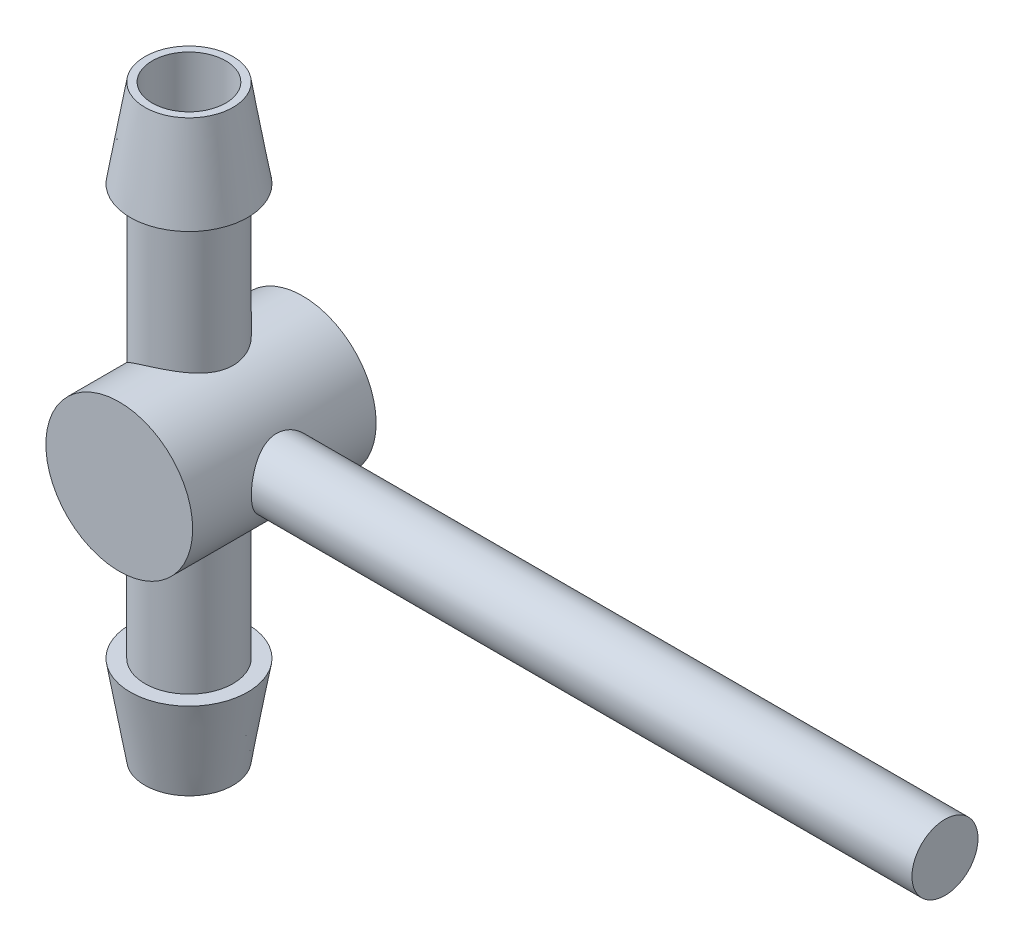
SolidWorks part; units mm, degrees
ref_plane "Front Plane" through (0, 0, 0) normal (0, 0, 1) x (1, 0, 0)
ref_plane "Top Plane" through (0, 0, 0) normal (0, 1, 0) x (1, 0, 0)
ref_plane "Right Plane" through (0, 0, 0) normal (1, 0, 0) x (0, 0, -1)
sketch "Sketch1" plane through (0, 0, 0) normal (0, 0, 1) x (1, 0, 0)
  circle A0 centre (0, 0) radius 5
  dimension "D1" = 10
extrude "Boss-Extrude1" add sketch "Sketch1" along normal mid plane 12.5
sketch "Sketch2" plane through (0, 0, 0) normal (0, 1, 0) x (1, 0, 0)
  line L0 (-5, 6.25) -> (-5, -6.25) construction
  circle A0 centre (-1.5, 0) radius 3
  point P2 (0, 0)
  point P3 (0, 0)
  point P4 (0, 0)
  point P5 (0, 0)
  dimension "D1" = 6
  dimension "D2" = 3.5
extrude "Boss-Extrude2" add sketch "Sketch2" along normal mid plane 40
sketch "Sketch3" plane through (0, 0, 0) normal (1, 0, 0) x (0, 0, -1)
  circle A0 centre (0, 0) radius 2.25
  dimension "D1" = 4.5
extrude "Boss-Extrude3" add sketch "Sketch3" along normal blind 50
sketch "Sketch4" plane through (0, -20, 0) normal (0, -1, 0) x (1, 0, 0)
  line L0 (-5, 6.25) -> (-5, -6.25) construction
  circle A0 centre (-1.5, 0) radius 2.5
  point P3 (0, 0)
  dimension "D1" = 5
  dimension "D2" = 3.5
extrude "Cut-Extrude1" cut sketch "Sketch4" against normal up to next (40 mm away) from surface at 0 starting at face at (-1.5, -20, 3)
sketch "Sketch5" plane through (0, 0, 6.25) normal (0, 0, 1) x (1, 0, 0)
  circle A0 centre (0, 0) radius 3.75
  dimension "D1" = 7.5
extrude "Cut-Extrude2" cut sketch "Sketch5" against normal up to next
sketch "Sketch6" plane through (0, 0, 0) normal (0, 0, 1) x (1, 0, 0)
  line L0 (1.5, 20) -> (2.5, 14)
  line L1 (2.5, 14) -> (1.5, 14)
  line L2 (1.5, 4.7697) -> (1.5, 20) construction
  line L3 (1.5, 14) -> (1.5, 20)
  line L4 (-1.5, 20) -> (-1.5, -20)
  line L6 (1.5, -14) -> (1.5, -20)
  line L7 (1.5, -20) -> (2.5, -14)
  line L8 (2.5, -14) -> (1.5, -14)
  line L10 (1.5, 14) -> (1.5, 20)
  line L11 (2.5, 14) -> (1.5, 14)
  line L12 (1.5, -14) -> (2.5, -14)
  line L13 (1.5, -20) -> (2.5, -14)
  line L14 (1.5, -20) -> (1.5, -14)
  line L16 (-4.5, -20) -> (1.5, -20) construction
  line L17 (1.5, -20) -> (1.5, -4.7697) construction
  line L19 (1.5, 20) -> (-4.5, 20) construction
  dimension "D1" = 6
  dimension "D2" = 1
  dimension "D3" = 6
  dimension "D4" = 1
sketch "Sketch7" plane through (0, 0, 6.25) normal (0, 0, 1) x (1, 0, 0)
  circle A0 centre (0, 0) radius 5
extrude "Boss-Extrude4" add sketch "Sketch7" against normal blind 2.5
revolve "Revolve1" add sketch "Sketch6" angle 360 about L4
